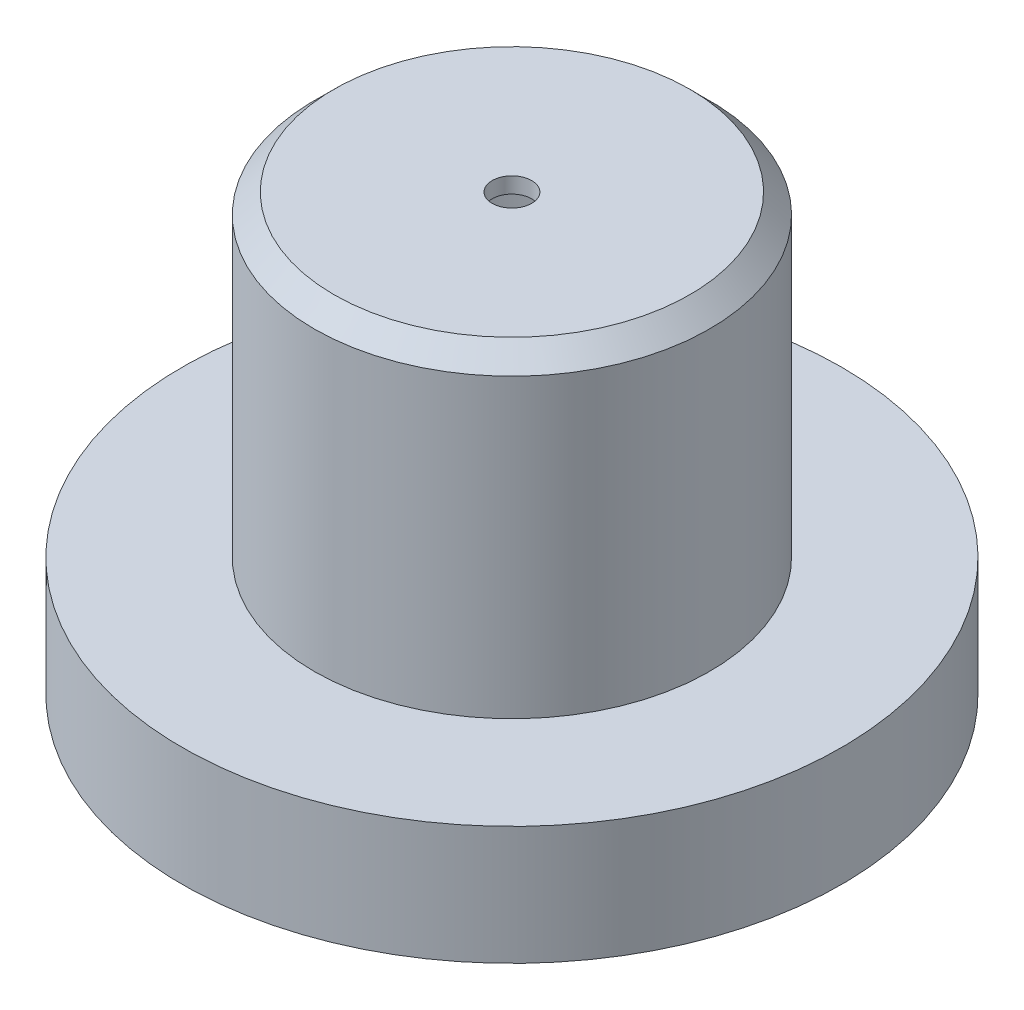
SolidWorks part; units mm, degrees
material "Alloy Steel"
ref_plane "Front Plane" through (0, 0, 0) normal (0, 0, 1) x (1, 0, 0)
ref_plane "Top Plane" through (0, 0, 0) normal (0, 1, 0) x (1, 0, 0)
ref_plane "Right Plane" through (0, 0, 0) normal (1, 0, 0) x (0, 0, -1)
sketch "Sketch2" plane through (0, 0, 0) normal (0, 0, 1) x (1, 0, 0)
  line L0 (55, 0) -> (-55, 0) construction
  line L1 (-75, 50) -> (-70, 50)
  line L2 (-75, 50) -> (-75, 15)
  line L3 (-75, -50) -> (-70, -50)
  line L4 (75, 50) -> (75, 15)
  line L5 (-75, 50) -> (75, -50) construction
  line L6 (-75, -50) -> (75, 50) construction
  line L7 (0, 50) -> (0, -74.3862) construction
  line L8 (-75, -15) -> (-75, -50)
  line L9 (75, -15) -> (75, -50)
  line L10 (-82.5762, 0) -> (133.8676, 0) construction
  line L11 (-60, 50) -> (-35, 50)
  line L12 (-25, 50) -> (25, 50)
  line L13 (35, 50) -> (60, 50)
  line L14 (70, 50) -> (75, 50)
  line L15 (-60, -50) -> (-35, -50)
  line L16 (-25, -50) -> (25, -50)
  line L17 (35, -50) -> (60, -50)
  line L18 (70, -50) -> (75, -50)
  line L19 (-35, 50) -> (-25, 50)
  line L20 (25, 50) -> (35, 50)
  arc A0 (-75, 15) -> (-75, -15) centre (-100.9808, 0) cw
  arc A1 (75, 15) -> (75, -15) centre (100.9808, 0) ccw
  arc A3 (-70, 50) -> (-60, 50) centre (-65, 50) ccw
  arc A4 (-35, -50) -> (-25, -50) centre (-30, -50) cw
  arc A5 (-70, -50) -> (-60, -50) centre (-65, -50) cw
  arc A6 (70, 50) -> (60, 50) centre (65, 50) cw
  arc A8 (70, -50) -> (60, -50) centre (65, -50) ccw
  arc A9 (35, -50) -> (25, -50) centre (30, -50) ccw
  point P0 (0, 0)
  dimension "D3" = 30
  dimension "D8" = 10
  dimension "D1" = 100
  dimension "D2" = 150
  dimension "D4" = 15
  dimension "D5" = 15
  dimension "D7" = 10
extrude "Boss-Extrude1" add sketch "Sketch2" along normal mid plane 200
sketch "Sketch3" plane through (0, 50, 0) normal (0, 1, 0) x (1, 0, 0)
  circle A0 centre (0, 0) radius 55
  circle A1 centre (0, 0) radius 50
  dimension "D1" = 110
  dimension "D2" = 100
extrude "Boss-Extrude3" add sketch "Sketch3" along normal blind 80 contours A1
chamfer "Chamfer1" distance 5 angle 45 1 edges at (0, 130, 50)
fillet "Fillet1" radius 1 4 edges at (75, -50, 0) (-75, -50, 0) (-75, 50, 0) (75, 50, 0)
sketch "Sketch4" plane through (0, -50, 0) normal (0, -1, 0) x (1, 0, 0)
  line L0 (132, 0) -> (-132, 0) construction
  line L1 (0, -132) -> (0, 132) construction
  circle A0 centre (-47.5, 80) radius 5
  circle A1 centre (47.5, 80) radius 5
  circle A2 centre (47.5, 40) radius 5
  circle A3 centre (47.5, 0) radius 5
  circle A4 centre (47.5, -40) radius 5
  circle A5 centre (47.5, -80) radius 5
  circle A6 centre (-47.5, 40) radius 5
  circle A7 centre (-47.5, 0) radius 5
  circle A8 centre (-47.5, -40) radius 5
  circle A9 centre (-47.5, -80) radius 5
  dimension "D3" = 10
  dimension "D1" = 80
  dimension "D2" = 47.5
  dimension "D4" = 2
  dimension "D5" = 5
extrude "Cut-Extrude1" cut sketch "Sketch4" against normal blind 20
sketch "Sketch5" plane through (0, 0, -100) normal (0, 0, -1) x (-1, 0, 0)
  line L0 (132, 0) -> (-132, 0) construction
  line L1 (-55, -15) -> (5, -15)
  line L2 (-55, -15) -> (-55, -25)
  line L3 (-55, -25) -> (5, -25)
  line L4 (5, -15) -> (5, -25)
  line L5 (-55, -15) -> (5, -25) construction
  line L6 (-55, -25) -> (5, -15) construction
  line L7 (-50, 15) -> (0, 15)
  line L8 (-50, 15) -> (-50, 5)
  line L9 (-50, 5) -> (0, 5)
  line L10 (0, 15) -> (0, 5)
  line L11 (-50, 15) -> (0, 5) construction
  line L12 (-50, 5) -> (0, 15) construction
  line L13 (0, 132) -> (0, -132) construction
  circle A0 centre (40, 25) radius 15
  circle A1 centre (35, 25) radius 2.5
  circle A2 centre (45, 25) radius 2.5
  point P0 (-25, -20)
  point P5 (-25, 10)
  dimension "D13" = 30
  dimension "D14" = 5
  dimension "D15" = 5
  dimension "D1" = 25
  dimension "D2" = 40
  dimension "D3" = 5
  dimension "D4" = 5
  dimension "D5" = 10
  dimension "D6" = 25
  dimension "D7" = 20
  dimension "D8" = 25
  dimension "D9" = 10
  dimension "D10" = 50
  dimension "D11" = 60
  dimension "D12" = 10
extrude "Cut-Extrude2" cut sketch "Sketch5" against normal blind 20
sketch "Sketch6" plane through (0, 50, 0) normal (0, 1, 0) x (1, 0, 0)
  line L1 (-75, 100) -> (75, 100)
  line L2 (-75, 100) -> (-75, -100)
  line L3 (-75, -100) -> (75, -100)
  line L4 (75, 100) -> (75, -100)
extrude "Cut-Extrude3" cut sketch "Sketch6" against normal blind 181
sketch "Sketch7" plane through (0, 50, 0) normal (0, -1, 0) x (1, 0, 0)
  circle A0 centre (0, 0) radius 83.3335
  dimension "D1" = 166.667
extrude "Boss-Extrude4" add sketch "Sketch7" along normal blind 30
sketch "Sketch8" plane through (0, 20, 0) normal (0, -1, 0) x (1, 0, 0)
  circle A0 centre (0, 0) radius 115
sketch "Sketch9" plane through (0, 130, 0) normal (0, 1, 0) x (1, 0, 0)
  circle A0 centre (0, 0) radius 5
shell "Shell1" thickness 4
sketch "Sketch10" plane through (0, 130, 0) normal (0, 1, 0) x (1, 0, 0)
  circle A0 centre (0, 0) radius 5
extrude "Cut-Extrude4" cut sketch "Sketch10" against normal blind 209
sketch "Sketch11" plane through (0, 130, 0) normal (0, 1, 0) x (1, 0, 0)
